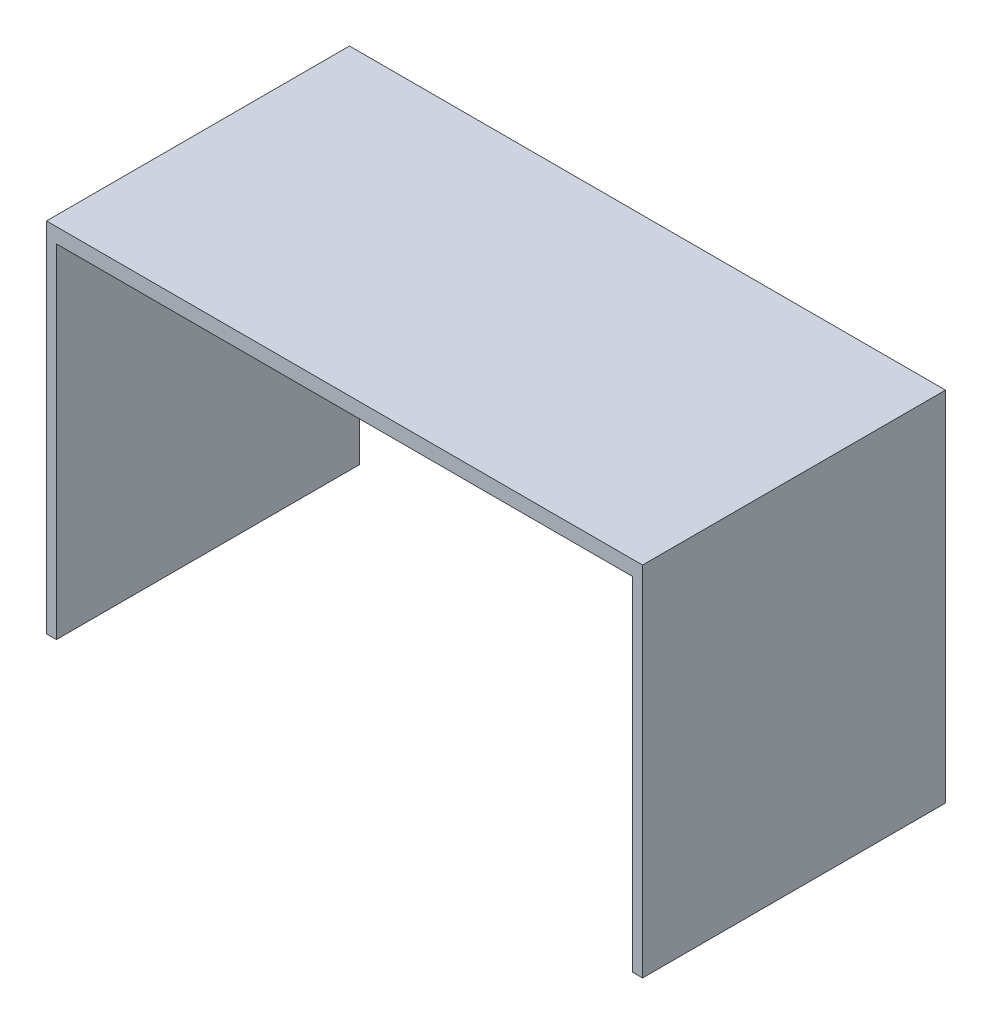
SolidWorks part; units mm, degrees
ref_plane "Front Plane" through (0, 0, 0) normal (0, 0, 1) x (1, 0, 0)
ref_plane "Top Plane" through (0, 0, 0) normal (0, 1, 0) x (1, 0, 0)
ref_plane "Right Plane" through (0, 0, 0) normal (1, 0, 0) x (0, 0, -1)
sketch "Sketch1" plane through (0, 0, 0) normal (0, 1, 0) x (1, 0, 0)
  line L1 (-762, -387.35) -> (762, -387.35)
  line L2 (-762, -387.35) -> (-762, 387.35)
  line L3 (-762, 387.35) -> (762, 387.35)
  line L4 (762, -387.35) -> (762, 387.35)
  line L5 (-762, -387.35) -> (762, 387.35) construction
  line L6 (-762, 387.35) -> (762, -387.35) construction
  point P0 (0, 0)
  dimension "D1" = 774.7
  dimension "D2" = 1524
extrude "Boss-Extrude1" add sketch "Sketch1" along normal blind 914.4
sketch "Sketch2" plane through (0, 0, 387.35) normal (0, 0, 1) x (1, 0, 0)
  line L0 (-762, 0) -> (762, 0) construction
  line L1 (-736.6, 0) -> (736.6, 0)
  line L2 (-736.6, 0) -> (-736.6, 876.3)
  line L3 (-736.6, 876.3) -> (736.6, 876.3)
  line L4 (736.6, 0) -> (736.6, 876.3)
  line L5 (-762, 914.4) -> (-762, 0) construction
  line L6 (762, 914.4) -> (762, 0) construction
  line L7 (-762, 914.4) -> (762, 914.4) construction
  dimension "D1" = 25.4
  dimension "D2" = 25.4
  dimension "D3" = 38.1
extrude "Cut-Extrude1" cut sketch "Sketch2" against normal blind 889
